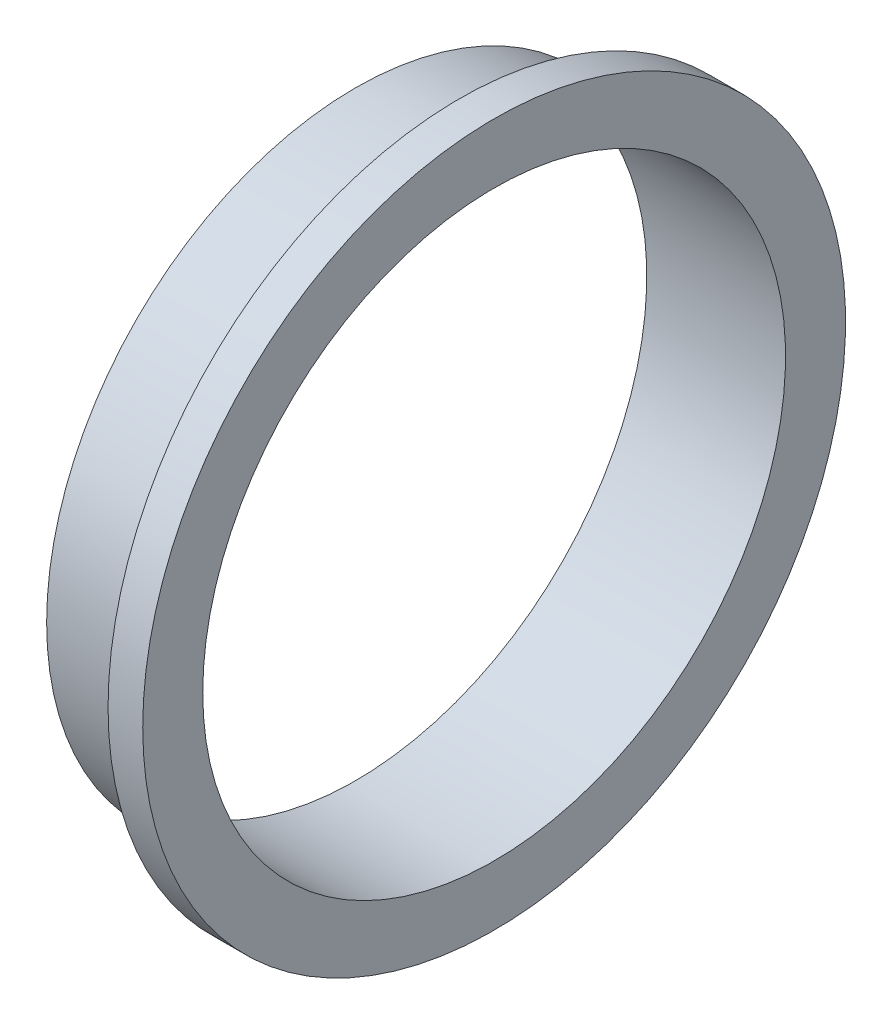
SolidWorks part; units mm, degrees
ref_plane "Front Plane" through (0, 0, 0) normal (0, 0, 1) x (1, 0, 0)
ref_plane "Top Plane" through (0, 0, 0) normal (0, 1, 0) x (1, 0, 0)
ref_plane "Right Plane" through (0, 0, 0) normal (1, 0, 0) x (0, 0, -1)
sketch "Sketch1" plane through (0, 0, 0) normal (0, 0, 1) x (1, 0, 0)
  line L0 (0, 89) -> (30, 89)
  line L1 (30, 89) -> (30, 101.3)
  line L2 (30, 101.3) -> (40, 101.3)
  line L3 (0, 89) -> (0, 84)
  line L4 (0, 84) -> (40, 84)
  line L5 (40, 84) -> (40, 101.3)
  dimension "D1" = 89
ref_axis "Axis1" through (-2, 0, 0) along (1, 0, 0)
revolve "Revolve1" add sketch "Sketch1" angle 360 about axis through (-2, 0, 0) along (1, 0, 0)
